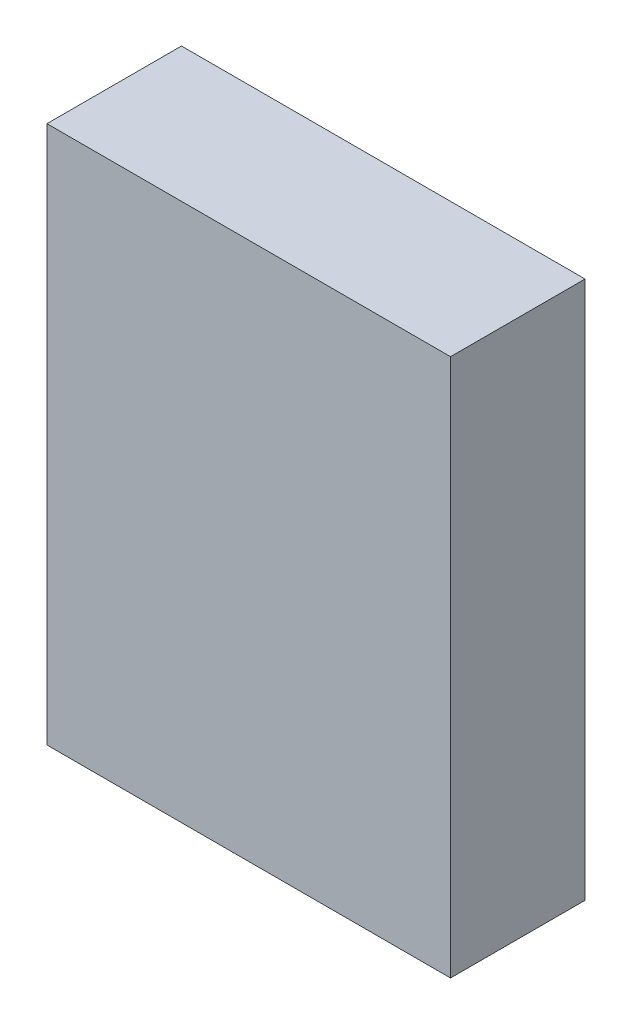
SolidWorks part; units mm, degrees
ref_plane "Front Plane" through (0, 0, 0) normal (0, 0, 1) x (1, 0, 0)
ref_plane "Top Plane" through (0, 0, 0) normal (0, 1, 0) x (1, 0, 0)
ref_plane "Right Plane" through (0, 0, 0) normal (1, 0, 0) x (0, 0, -1)
sketch "Sketch1" plane through (0, 0, 0) normal (0, 0, 1) x (1, 0, 0)
  line L1 (-7.5, -10) -> (7.5, -10)
  line L2 (-7.5, -10) -> (-7.5, 10)
  line L3 (-7.5, 10) -> (7.5, 10)
  line L4 (7.5, -10) -> (7.5, 10)
  line L5 (0, 10) -> (0, -10) construction
  line L6 (-7.5, 0) -> (7.5, 0) construction
  point P0 (0, 0)
  dimension "D1" = 15
  dimension "D2" = 20
extrude "Boss-Extrude1" add sketch "Sketch1" along normal blind 5
